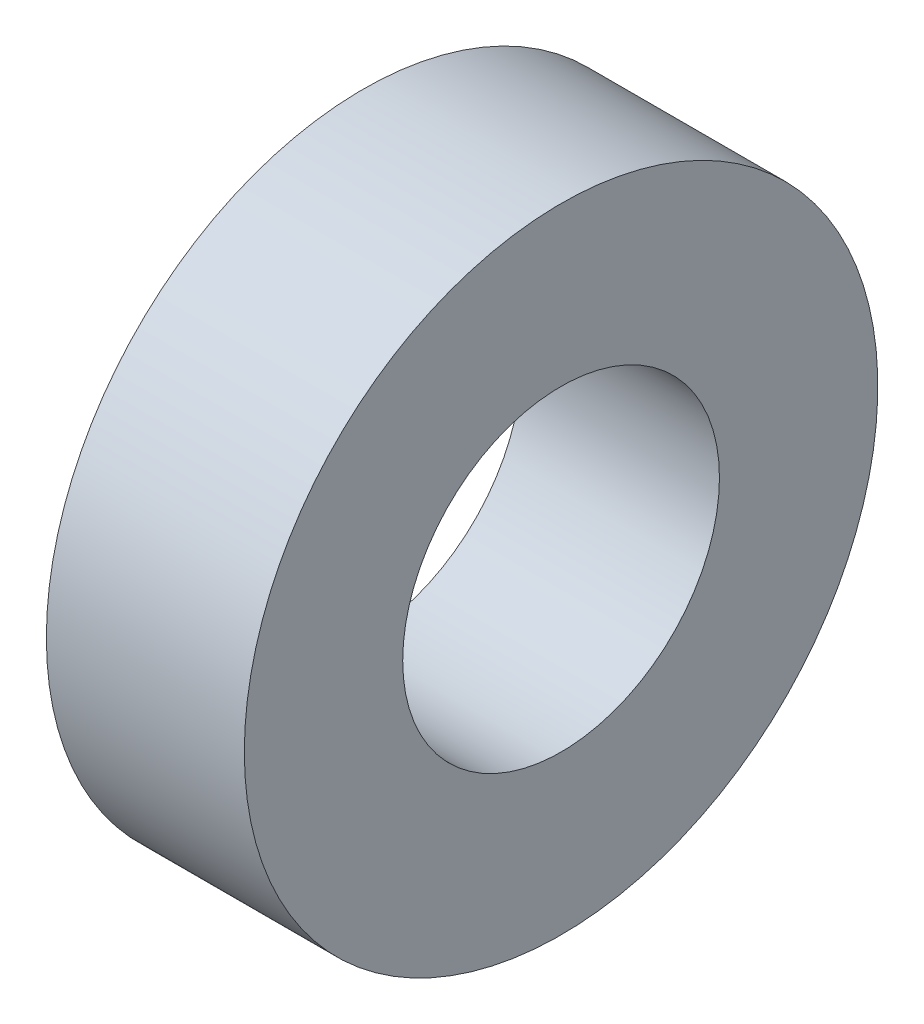
SolidWorks part; units mm, degrees
ref_plane "Front Plane" through (0, 0, 0) normal (0, 0, 1) x (1, 0, 0)
ref_plane "Top Plane" through (0, 0, 0) normal (0, 1, 0) x (1, 0, 0)
ref_plane "Right Plane" through (0, 0, 0) normal (1, 0, 0) x (0, 0, -1)
sketch "Sketch1" plane through (0, 0, 0) normal (0, 0, 1) x (1, 0, 0)
  line L0 (-188.1922, 0) -> (9221.4174, 0) construction
  line L1 (0, 4) -> (0, 8)
  line L2 (0, 8) -> (5, 8)
  line L3 (5, 8) -> (5, 4)
  line L4 (5, 4) -> (0, 4)
  dimension "D1" = 16
  dimension "D2" = 5
  dimension "D3" = 8
revolve "Revolve1" add sketch "Sketch1" angle 360 about L0
